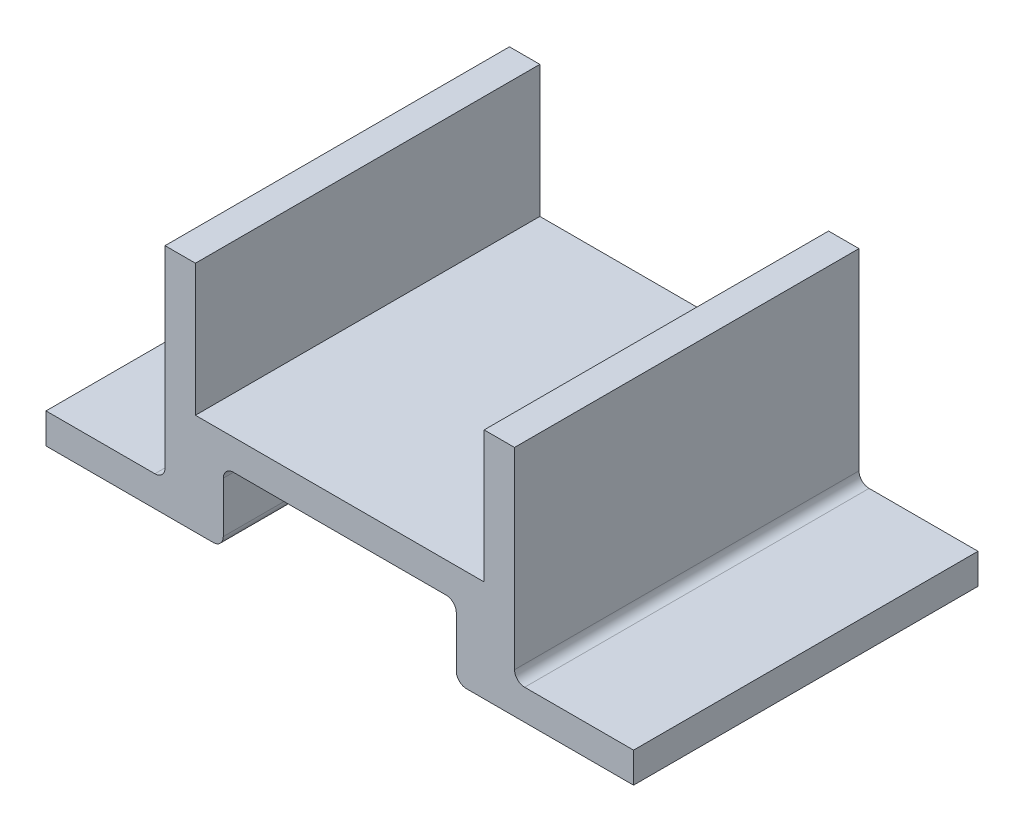
SolidWorks part; units mm, degrees
ref_plane "Front Plane" through (0, 0, 0) normal (0, 0, 1) x (1, 0, 0)
ref_plane "Top Plane" through (0, 0, 0) normal (0, 1, 0) x (1, 0, 0)
ref_plane "Right Plane" through (0, 0, 0) normal (1, 0, 0) x (0, 0, -1)
sketch "Sketch1" plane through (0, 0, 0) normal (0, 1, 0) x (1, 0, 0)
  line L1 (-29, -17) -> (29, -17)
  line L2 (-29, -17) -> (-29, 17)
  line L3 (-29, 17) -> (29, 17)
  line L4 (29, -17) -> (29, 17)
  line L5 (-29, -17) -> (29, 17) construction
  line L6 (-29, 17) -> (29, -17) construction
  point P0 (0, 0)
  dimension "D1" = 58
  dimension "D2" = 34
extrude "Boss-Extrude1" add sketch "Sketch1" along normal blind 10
sketch "Sketch3" plane through (0, 0, 17) normal (0, 0, 1) x (1, 0, 0)
  line L0 (-29, 0) -> (29, 0) construction
  line L1 (-11.5, 7) -> (11.5, 7)
  line L2 (-11.5, 7) -> (-11.5, 0)
  line L3 (-11.5, 0) -> (11.5, 0)
  line L4 (11.5, 7) -> (11.5, 0)
  point P6 (0, 0)
  dimension "D1" = 7
  dimension "D2" = 23
extrude "Cut-Extrude1" cut sketch "Sketch3" against normal up to surface (34 mm away) up to face at (0, 5, -17)
sketch "Sketch4" plane through (0, 0, 17) normal (0, 0, 1) x (1, 0, 0)
  line L0 (-29, 10) -> (29, 10) construction
  line L1 (17.25, 10) -> (29, 10)
  line L2 (17.25, 10) -> (17.25, 3)
  line L3 (17.25, 3) -> (29, 3)
  line L4 (29, 10) -> (29, 3)
  line L5 (29, 10) -> (29, 0) construction
  line L6 (11.5, 0) -> (29, 0) construction
  line L7 (11.5, 0) -> (11.5, 7) construction
  dimension "D1" = 3
  dimension "D2" = 5.75
extrude "Cut-Extrude2" cut sketch "Sketch4" against normal up to surface (34 mm away) up to face at (0, 4.25, -17)
mirror "Mirror1" about plane through (0, 0, 0) normal (1, 0, 0) of "Cut-Extrude2"
sketch "Sketch6" plane through (0, 10, 0) normal (0, 1, 0) x (1, 0, 0)
  line L0 (17.25, 17) -> (-17.25, 17) construction
  line L1 (14.25, 17) -> (17.25, 17)
  line L2 (14.25, 17) -> (14.25, -17)
  line L3 (14.25, -17) -> (17.25, -17)
  line L4 (17.25, 17) -> (17.25, -17)
  line L5 (-17.25, -17) -> (17.25, -17) construction
  line L6 (17.25, 17) -> (17.25, -17) construction
  dimension "D1" = 3
extrude "Boss-Extrude2" add sketch "Sketch6" along normal blind 13
mirror "Mirror2" about plane through (0, 0, 0) normal (1, 0, 0) of "Boss-Extrude2"
fillet "Fillet1" radius 1 6 edges at (11.5, 7, 0) (-11.5, 7, 0) (17.25, 3, 0) (-17.25, 3, 0) (-11.5, 0, 0) (11.5, 0, 0)
